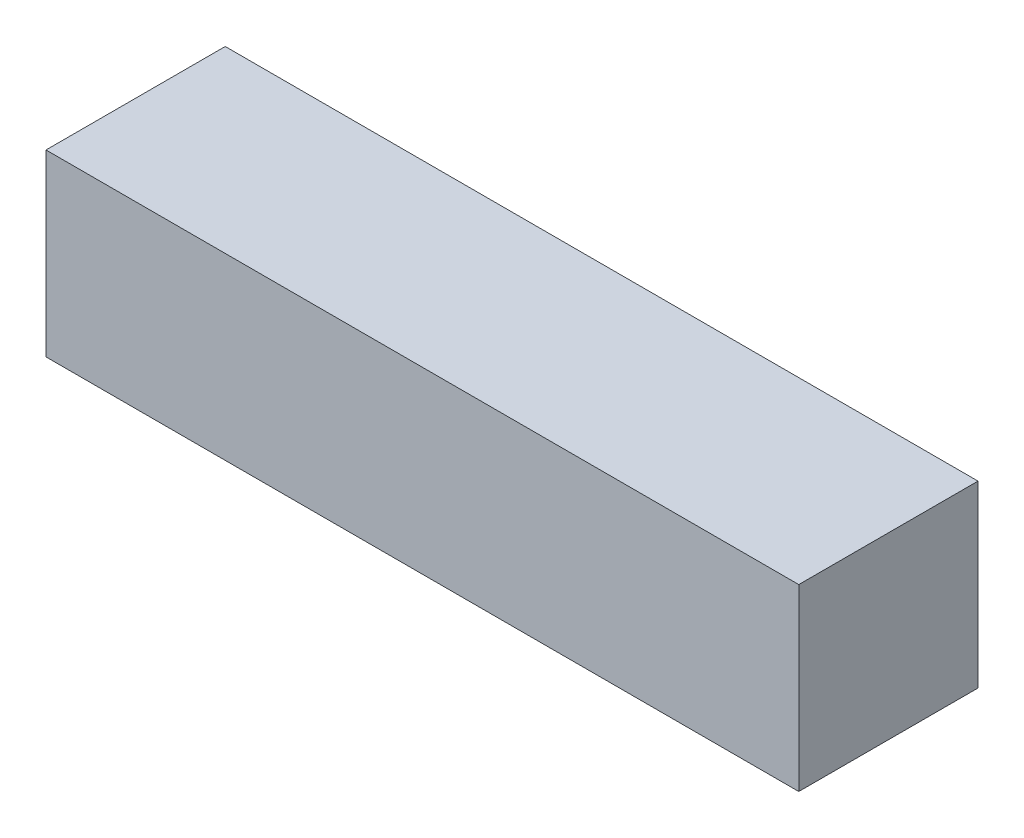
SolidWorks part; units mm, degrees
ref_plane "前基準面" through (0, 0, 0) normal (0, 0, 1) x (1, 0, 0)
ref_plane "上基準面" through (0, 0, 0) normal (0, 1, 0) x (1, 0, 0)
ref_plane "右基準面" through (0, 0, 0) normal (1, 0, 0) x (0, 0, -1)
sketch "草圖1" plane through (0, 0, 0) normal (0, 0, 1) x (1, 0, 0)
  line L1 (-24.0943, 8.2137) -> (17.9057, 8.2137)
  line L2 (-24.0943, 8.2137) -> (-24.0943, -1.7863)
  line L3 (-24.0943, -1.7863) -> (17.9057, -1.7863)
  line L4 (17.9057, 8.2137) -> (17.9057, -1.7863)
  dimension "D1" = 42
  dimension "D2" = 10
extrude "填料-伸長1" add sketch "草圖1" along normal blind 10
